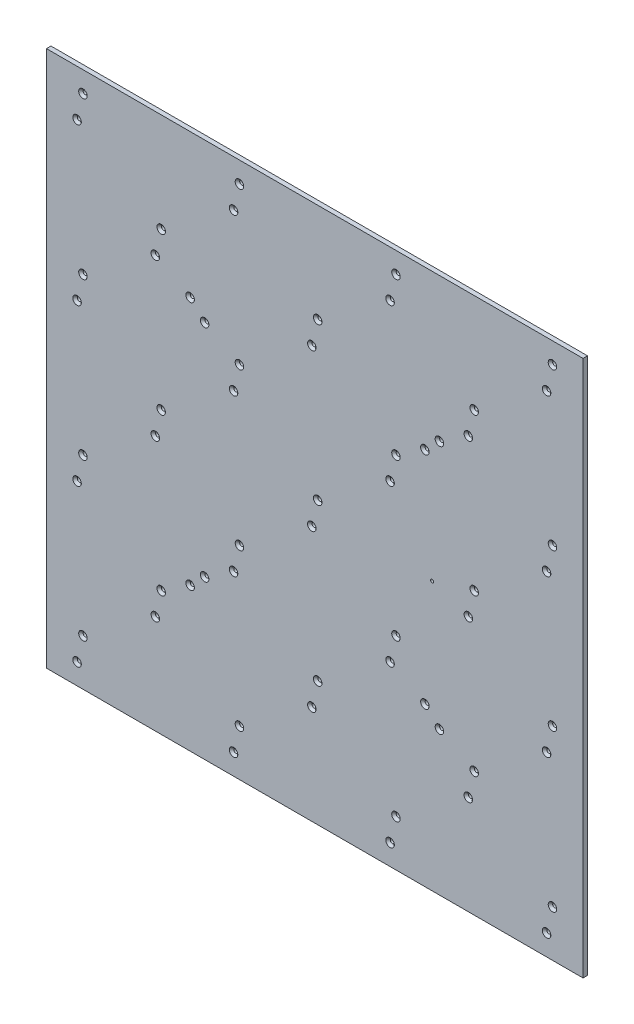
SolidWorks part; units mm, degrees
material "6063-T1"
ref_plane "Front Plane" through (0, 0, 0) normal (0, 0, 1) x (1, 0, 0)
ref_plane "Top Plane" through (0, 0, 0) normal (0, 1, 0) x (1, 0, 0)
ref_plane "Right Plane" through (0, 0, 0) normal (1, 0, 0) x (0, 0, -1)
sketch "Sketch1" plane through (0, 0, 0) normal (0, 0, 1) x (1, 0, 0)
  line L1 (600, -600) -> (-600, -600)
  line L2 (600, -600) -> (600, 600)
  line L3 (600, 600) -> (-600, 600)
  line L4 (-600, -600) -> (-600, 600)
  line L5 (600, -600) -> (-600, 600) construction
  line L6 (600, 600) -> (-600, -600) construction
  point P0 (0, 0)
  dimension "D1" = 1200
  dimension "D2" = 1200
extrude "Boss-Extrude1" add sketch "Sketch1" against normal blind 10 from offset 3
sketch "Sketch2" plane through (0, 0, -7) normal (0, 0, -1) x (-1, 0, 0)
  line L0 (-261.4393, 263.5607) -> (-244.8089, 280.1911) construction
  line L2 (-268.1434, 303.5257) -> (-221.4743, 256.8566) construction
  circle A1 centre (-278.75, 278.7769) radius 4.5
  circle A2 centre (-246.2231, 246.25) radius 4.5
  circle A3 centre (246.25, 246.2231) radius 4.5
  circle A4 centre (278.7769, 278.75) radius 4.5
  circle A5 centre (246.2231, -246.25) radius 4.5
  circle A6 centre (278.75, -278.7769) radius 4.5
  circle A7 centre (-246.25, -246.2231) radius 4.5
  circle A8 centre (-278.7769, -278.75) radius 4.5
  circle A9 centre (-531.5817, 553.5131) radius 4.5
  circle A10 centre (-518.4295, 496.5203) radius 4.5
  circle A11 centre (-531.5817, 203.5094) radius 4.5
  circle A12 centre (-518.4295, 146.5166) radius 4.5
  circle A13 centre (-343.4276, 321.5185) radius 4.5
  circle A14 centre (-356.5798, 378.5113) radius 4.5
  circle A15 centre (-181.578, 553.5131) radius 4.5
  circle A16 centre (-168.4258, 496.5203) radius 4.5
  circle A17 centre (168.4258, 553.5131) radius 4.5
  circle A18 centre (181.578, 496.5203) radius 4.5
  circle A19 centre (-6.5761, 378.5113) radius 4.5
  circle A20 centre (6.5761, 321.5185) radius 4.5
  circle A21 centre (-181.578, 203.5094) radius 4.5
  circle A22 centre (-168.4258, 146.5166) radius 4.5
  circle A23 centre (-356.5798, 28.5075) radius 4.5
  circle A24 centre (-343.4276, -28.4853) radius 4.5
  circle A25 centre (-518.4295, -203.4871) radius 4.5
  circle A26 centre (-531.5817, -146.4943) radius 4.5
  circle A27 centre (-531.5817, -496.498) radius 4.5
  circle A28 centre (-518.4295, -553.4908) radius 4.5
  circle A29 centre (-356.5798, -321.4962) radius 4.5
  circle A30 centre (-343.4276, -378.489) radius 4.5
  circle A31 centre (-181.578, -146.4943) radius 4.5
  circle A32 centre (-168.4258, -203.4871) radius 4.5
  circle A33 centre (-6.5761, 28.5075) radius 4.5
  circle A34 centre (6.5761, -28.4853) radius 4.5
  circle A35 centre (168.4258, 203.5094) radius 4.5
  circle A36 centre (181.578, 146.5166) radius 4.5
  circle A37 centre (343.4276, 378.5113) radius 4.5
  circle A38 centre (356.5798, 321.5185) radius 4.5
  circle A39 centre (518.4295, 553.5131) radius 4.5
  circle A40 centre (531.5817, 496.5203) radius 4.5
  circle A41 centre (-181.578, -496.498) radius 4.5
  circle A42 centre (-168.4258, -553.4908) radius 4.5
  circle A43 centre (-6.5761, -321.4962) radius 4.5
  circle A44 centre (6.5761, -378.489) radius 4.5
  circle A45 centre (168.4258, -146.4943) radius 4.5
  circle A46 centre (181.578, -203.4871) radius 4.5
  circle A47 centre (343.4276, 28.5075) radius 4.5
  circle A48 centre (356.5798, -28.4853) radius 4.5
  circle A49 centre (518.4295, 203.5094) radius 4.5
  circle A50 centre (531.5817, 146.5166) radius 4.5
  circle A51 centre (168.4258, -496.498) radius 4.5
  circle A52 centre (181.578, -553.4908) radius 4.5
  circle A53 centre (343.4276, -321.4962) radius 4.5
  circle A54 centre (356.5798, -378.489) radius 4.5
  circle A55 centre (531.5817, -203.4871) radius 4.5
  circle A56 centre (518.4295, -146.4943) radius 4.5
  circle A57 centre (518.4295, -496.498) radius 4.5
  circle A58 centre (531.5817, -553.4908) radius 4.5
  point P25 (0, 0)
  dimension "D1" = 9
  dimension "D2" = 4
extrude "Cut-Extrude1" cut sketch "Sketch2" against normal through all
chamfer "Chamfer1" distance 5 angle 45 58 edges at (250.7231, 246.25, 3) (274.25, 278.7769, 3) (-241.75, 246.2231, 3) (-283.2769, 278.75, 3) (-241.7231, -246.25, 3) (-283.25, -278.7769, 3) (250.75, -246.2231, 3) (274.2769, -278.75, 3) (527.0817, 553.5131, 3) (513.9295, 496.5203, 3) (527.0817, 203.5094, 3) (513.9295, 146.5166, 3) (338.9276, 321.5185, 3) (352.0798, 378.5113, 3) (177.078, 553.5131, 3) (163.9258, 496.5203, 3) (-172.9258, 553.5131, 3) (-186.078, 496.5203, 3) (2.0761, 378.5113, 3) (-11.0761, 321.5185, 3) (177.078, 203.5094, 3) (163.9258, 146.5166, 3) (352.0798, 28.5075, 3) (338.9276, -28.4853, 3) (513.9295, -203.4871, 3) (527.0817, -146.4943, 3) (527.0817, -496.498, 3) (513.9295, -553.4908, 3) (352.0798, -321.4962, 3) (338.9276, -378.489, 3) (177.078, -146.4943, 3) (163.9258, -203.4871, 3) (2.0761, 28.5075, 3) (-11.0761, -28.4853, 3) (-172.9258, 203.5094, 3) (-186.078, 146.5166, 3) (-347.9276, 378.5113, 3) (-361.0798, 321.5185, 3) (-522.9295, 553.5131, 3) (-536.0817, 496.5203, 3) (177.078, -496.498, 3) (163.9258, -553.4908, 3) (2.0761, -321.4962, 3) (-11.0761, -378.489, 3) (-172.9258, -146.4943, 3) (-186.078, -203.4871, 3) (-347.9276, 28.5075, 3) (-361.0798, -28.4853, 3) (-522.9295, 203.5094, 3) (-536.0817, 146.5166, 3) (-172.9258, -496.498, 3) (-186.078, -553.4908, 3) (-347.9276, -321.4962, 3) (-361.0798, -378.489, 3) (-536.0817, -203.4871, 3) (-522.9295, -146.4943, 3) (-522.9295, -496.498, 3) (-536.0817, -553.4908, 3)
sketch "Sketch3" plane through (0, 0, -7) normal (0, 0, -1) x (-1, 0, 0)
  line L0 (0, 0) -> (-525, 0) construction
  circle A0 centre (-262.5, 0) radius 3.4
  dimension "D1" = 6.8
extrude "Cut-Extrude2" cut sketch "Sketch3" against normal up to next
sketch "Sketch5" plane through (0, 0, 3) normal (0, 0, 1) x (1, 0, 0)
  line L0 (-350, 525) -> (-350, -525) construction
  line L1 (-525, 525) -> (525, 525) construction
  line L2 (-525, 525) -> (-525, -525) construction
  line L3 (-525, -525) -> (525, -525) construction
  line L4 (525, 525) -> (525, -525) construction
  line L5 (-525, 525) -> (525, -525) construction
  line L6 (-525, -525) -> (525, 525) construction
  line L7 (-175, 525) -> (-175, -525) construction
  line L8 (0, 525) -> (0, -525) construction
  line L9 (175, 525) -> (175, -525) construction
  line L10 (350, 525) -> (350, -525) construction
  line L11 (-525, 350) -> (525, 350) construction
  line L12 (-525, 175) -> (525, 175) construction
  line L13 (-525, 0) -> (525, 0) construction
  line L14 (-525, -175) -> (525, -175) construction
  line L15 (-525, -350) -> (525, -350) construction
  line L16 (175, 350) -> (350, 175) construction
  line L17 (350, -175) -> (175, -350) construction
  line L18 (-175, -350) -> (-350, -175) construction
  line L19 (-350, 175) -> (-175, 350) construction
  line L21 (339.3934, -45.9619) -> (304.0381, -10.6066) construction
  line L22 (339.3934, -45.9619) -> (395.9619, 10.6066) construction
  line L23 (395.9619, 10.6066) -> (360.6066, 45.9619) construction
  line L24 (304.0381, -10.6066) -> (360.6066, 45.9619) construction
  line L25 (339.3934, -45.9619) -> (360.6066, 45.9619) construction
  line L26 (395.9619, 10.6066) -> (304.0381, -10.6066) construction
  point P0 (0, 0)
  point P30 (350, 0)
  point P37 (0, 0)
  dimension "D1" = 1050
  dimension "D3" = 175
  dimension "D5" = 175
  dimension "D7" = 50
  dimension "D8" = 80
  dimension "D2" = 6
  dimension "D4" = 6
  dimension "D6" = 4
